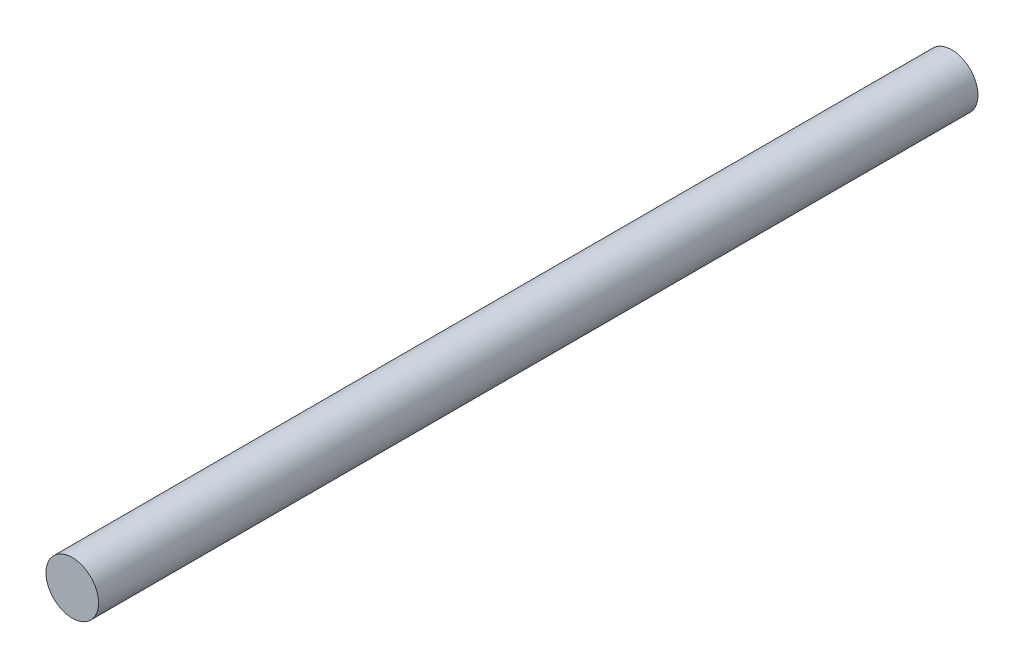
SolidWorks part; units mm, degrees
ref_plane "Front Plane" through (0, 0, 0) normal (0, 0, 1) x (1, 0, 0)
ref_plane "Top Plane" through (0, 0, 0) normal (0, 1, 0) x (1, 0, 0)
ref_plane "Right Plane" through (0, 0, 0) normal (1, 0, 0) x (0, 0, -1)
sketch "Sketch1" plane through (0, 0, 0) normal (0, 0, 1) x (1, 0, 0)
  circle A0 centre (0, 0) radius 3.9878
  dimension "D1" = 7.9756
extrude "Boss-Extrude1" add sketch "Sketch1" along normal blind 133.35 contours A0
